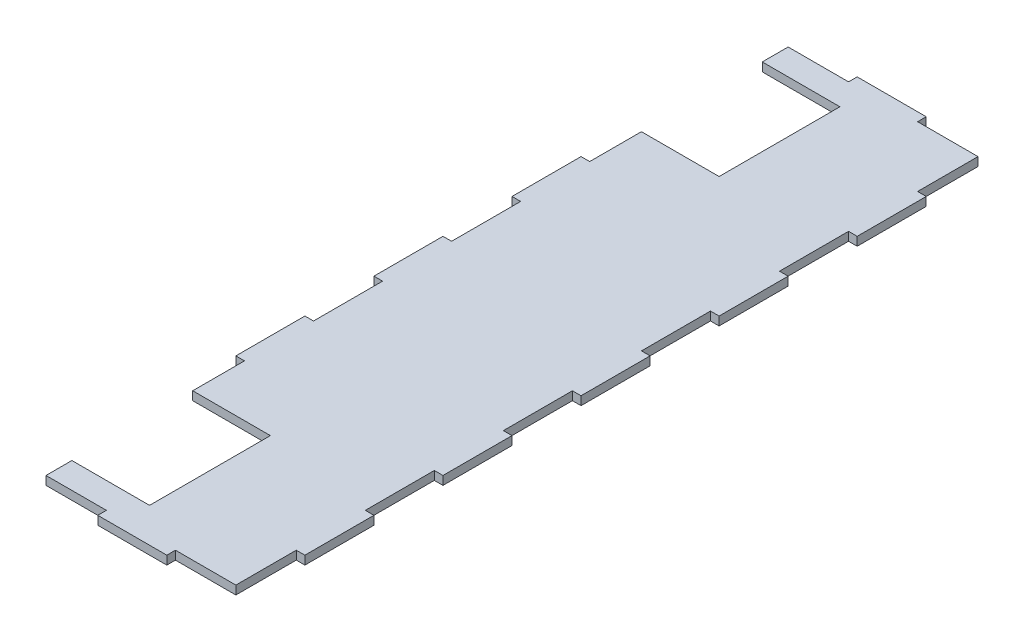
SolidWorks part; units mm, degrees
ref_plane "Front Plane" through (0, 0, 0) normal (0, 0, 1) x (1, 0, 0)
ref_plane "Top Plane" through (0, 0, 0) normal (0, 1, 0) x (1, 0, 0)
ref_plane "Right Plane" through (0, 0, 0) normal (1, 0, 0) x (0, 0, -1)
sketch "Sketch1" plane through (0, 0, 0) normal (0, 1, 0) x (1, 0, 0)
  line L0 (0, 0) -> (-38.1, 0)
  line L2 (-34.925, 38.1) -> (-38.1, 38.1)
  line L3 (-38.1, 38.1) -> (-38.1, 63.5)
  line L4 (-38.1, 63.5) -> (-34.925, 63.5)
  line L5 (-34.925, 63.5) -> (-34.925, 88.9)
  line L6 (-34.925, 88.9) -> (-38.1, 88.9)
  line L7 (-38.1, 88.9) -> (-38.1, 114.3)
  line L8 (-38.1, 114.3) -> (-34.925, 114.3)
  line L9 (-34.925, 114.3) -> (-34.925, 136.525)
  line L10 (0, 0) -> (0, 139.7)
  line L13 (0, 139.7) -> (-12.7, 139.7)
  line L14 (-12.7, 139.7) -> (-12.7, 136.525)
  line L15 (-12.7, 136.525) -> (-34.925, 136.525)
  line L16 (-34.925, 38.1) -> (-34.925, 12.7)
  line L17 (-34.925, 12.7) -> (-38.1, 12.7)
  line L18 (-38.1, 12.7) -> (-38.1, 0)
  point P14 (0, 0)
  point P18 (-39.0136, 1.1895)
  point P20 (-34.7742, 0)
  point P21 (-37.0785, 0)
  point P22 (-36.5802, 0)
  dimension "D1" = 12.7
  dimension "D2" = 12.7
  dimension "D3" = 3.175
  dimension "D4" = 22.225
  dimension "D5" = 22.225
  dimension "D6" = 25.4
extrude "Boss-Extrude1" add sketch "Sketch1" along normal blind 3.175 contours L0 L18 L17 L16 L2 L3 L4 L5 L6 L7 L8 L9 L15 L14 L13 L10
mirror "Mirror1" about plane through (0, 3.175, 0) normal (-1, 0, 0) of bodies 105
sketch "Sketch2" plane through (0, 3.175, 0) normal (0, 1, 0) x (1, 0, 0)
  line L0 (12.7, 139.7) -> (-12.7, 139.7) construction
  line L1 (-6.35, 127) -> (-38.1, 127)
  line L2 (-6.35, 127) -> (-6.35, 82.55)
  line L3 (-6.35, 82.55) -> (-38.1, 82.55)
  line L4 (-38.1, 127) -> (-38.1, 82.55)
  line L5 (-38.1, 88.9) -> (-38.1, 114.3) construction
  dimension "D1" = 44.45
  dimension "D2" = 12.7
  dimension "D3" = 31.75
extrude "Cut-Extrude1" cut sketch "Sketch2" against normal through all both and the other way through all
mirror "Mirror2" about plane through (0, 3.175, 0) normal (0, 0, 1) of bodies 109
